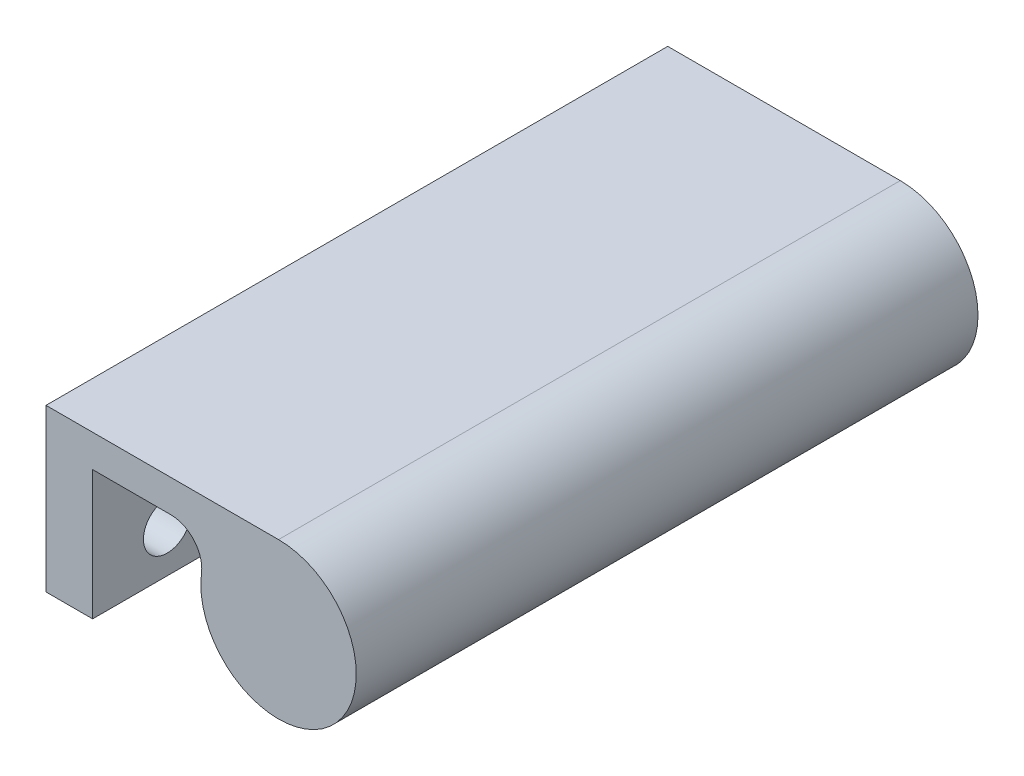
SolidWorks part; units mm, degrees
ref_plane "Front Plane" through (0, 0, 0) normal (1, 0, 0) x (0, 1, 0)
ref_plane "Top Plane" through (0, 0, 0) normal (0, 0, 1) x (0, 1, 0)
ref_plane "Right Plane" through (0, 0, 0) normal (0, 1, 0) x (-1, 0, 0)
ref_plane "Plane1"
sketch "Sketch1" plane through (0, 0, 0) normal (1, 0, 0) x (0, 1, 0)
  line L0 (0, -63.5) -> (16.51, -63.5)
  line L1 (16.51, -63.5) -> (16.51, 0)
  line L2 (16.51, 0) -> (0, 0)
  line L3 (0, 0) -> (0, -63.5)
  circle A0 centre (4.445, -7.62) radius 2.4329
  circle A1 centre (4.445, -15.6185) radius 2.4329
  circle A2 centre (4.445, -23.6169) radius 2.4329
  circle A3 centre (4.445, -31.6154) radius 2.4329
  circle A4 centre (4.445, -39.6138) radius 2.4329
  circle A5 centre (4.445, -47.6123) radius 2.4329
  circle A6 centre (4.445, -55.6108) radius 2.4329
  dimension "D1" = 63.5
  dimension "D2" = 16.51
  dimension "D3" = 7.9985
  dimension "D4" = 31.6154
extrude "Extrusion1" add sketch "Sketch1" along normal blind 4.7625 contours L2 L3 L0 L1 A6 A5 A4 A3 A2 A1 A0
sketch "Sketch2" plane through (4.7625, 0, 0) normal (1, 0, 0) x (0, 0, -1)
  line L0 (0, 13.208) -> (63.5, 13.208)
  line L1 (63.5, 13.208) -> (63.5, 16.51)
  line L2 (63.5, 16.51) -> (0, 16.51)
  line L3 (0, 16.51) -> (0, 13.208)
  dimension "D1" = 3.302
extrude "Extrusion2" add sketch "Sketch2" along normal blind 1.016
sketch "Sketch3" plane through (0, 0, 0) normal (0, 0, 1) x (1, 0, 0)
  line L0 (23.749, 16.51) -> (5.7785, 16.51)
  line L1 (5.7785, 16.51) -> (5.7785, 13.208)
  line L2 (5.7785, 13.208) -> (12.7329, 13.208)
  arc A0 (15.8804, 9.6157) -> (12.7329, 13.208) centre (12.7329, 10.033) ccw
  arc A1 (15.8804, 9.6157) -> (23.749, 16.51) centre (23.749, 8.5725) ccw
  dimension "D1" = 15.875
  dimension "D2" = 3.175
extrude "Extrusion3" add sketch "Sketch3" against normal blind 63.5
